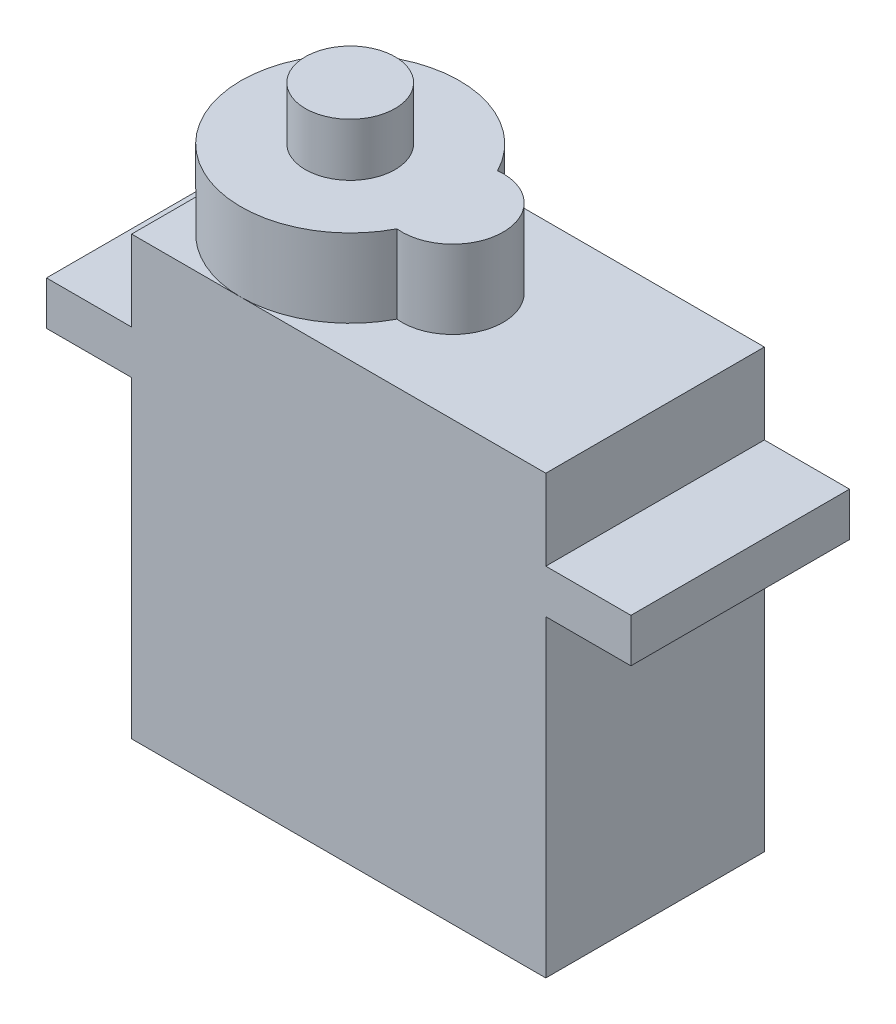
SolidWorks part; units mm, degrees
ref_plane "Front Plane" through (0, 0, 0) normal (0, 0, 1) x (1, 0, 0)
ref_plane "Top Plane" through (0, 0, 0) normal (0, 1, 0) x (1, 0, 0)
ref_plane "Right Plane" through (0, 0, 0) normal (1, 0, 0) x (0, 0, -1)
sketch "Sketch1" plane through (0, 0, 0) normal (0, 0, 1) x (1, 0, 0)
  line L0 (11.43, 24.13) -> (11.43, 0) construction
  line L1 (0, 0) -> (22.86, 0)
  line L2 (0, 0) -> (0, 17.272)
  line L3 (0, 24.13) -> (22.86, 24.13)
  line L4 (22.86, 0) -> (22.86, 17.272)
  line L5 (0, 19.685) -> (-4.699, 19.685)
  line L7 (0, 17.272) -> (-4.699, 17.272)
  line L8 (-4.699, 19.685) -> (-4.699, 17.272)
  line L9 (27.559, 19.685) -> (27.559, 17.272)
  line L10 (22.86, 17.272) -> (27.559, 17.272)
  line L12 (22.86, 19.685) -> (27.559, 19.685)
  line L13 (0, 19.685) -> (0, 24.13)
  line L14 (22.86, 19.685) -> (22.86, 24.13)
  dimension "D1" = 24.13
  dimension "D2" = 22.86
  dimension "D3" = 17.272
  dimension "D4" = 2.413
  dimension "D5" = 4.699
extrude "Boss-Extrude1" add sketch "Sketch1" along normal blind 12.065
ref_plane "Plane1" through (0, 24.13, 0) normal (0, 1, 0) x (1, 0, 0)
sketch "Sketch2" plane through (0, 24.13, 0) normal (0, 1, 0) x (1, 0, 0)
  line L0 (0, -6.0325) -> (14.478, -6.0325) construction
  line L1 (11.379, -3.2385) -> (11.684, -3.2385)
  line L2 (11.379, -8.8265) -> (11.684, -8.8265)
  line L4 (22.86, 0) -> (0, 0)
  line L5 (0, 0) -> (0, -12.065)
  line L6 (0, -12.065) -> (22.86, -12.065)
  line L7 (22.86, -12.065) -> (22.86, 0)
  line L8 (22.86, 0) -> (0, 0) construction
  line L9 (0, 0) -> (0, -12.065) construction
  line L10 (0, -12.065) -> (22.86, -12.065) construction
  line L11 (22.86, -12.065) -> (22.86, 0) construction
  arc A0 (11.3872, -3.2543) -> (11.3872, -8.8107) centre (6.0325, -6.0325) ccw
  arc A1 (11.3872, -8.8107) -> (11.3872, -3.2543) centre (11.684, -6.0325) ccw
  circle A2 centre (6.0325, -6.0325) radius 6.0325 construction
  dimension "D2" = 14.478
  dimension "D3" = 5.588
  dimension "D1" = 0
extrude "Boss-Extrude2" add sketch "Sketch2" along normal blind 4.318 contours A1 A0
sketch "Sketch3" plane through (0, 28.448, 0) normal (0, 1, 0) x (1, 0, 0)
  circle A0 centre (6.0325, -6.0325) radius 2.4765
  arc A2 (11.3872, -8.8107) -> (11.3872, -3.2543) centre (11.684, -6.0325) ccw
  arc A3 (11.3872, -3.2543) -> (11.3872, -8.8107) centre (6.0325, -6.0325) ccw
  arc A4 (11.3872, -8.8107) -> (11.3872, -3.2543) centre (11.684, -6.0325) ccw
  arc A5 (11.3872, -3.2543) -> (11.3872, -8.8107) centre (6.0325, -6.0325) ccw
  dimension "D2" = 4.953
  dimension "D1" = 0
extrude "Boss-Extrude3" add sketch "Sketch3" along normal blind 2.921 contours A0
